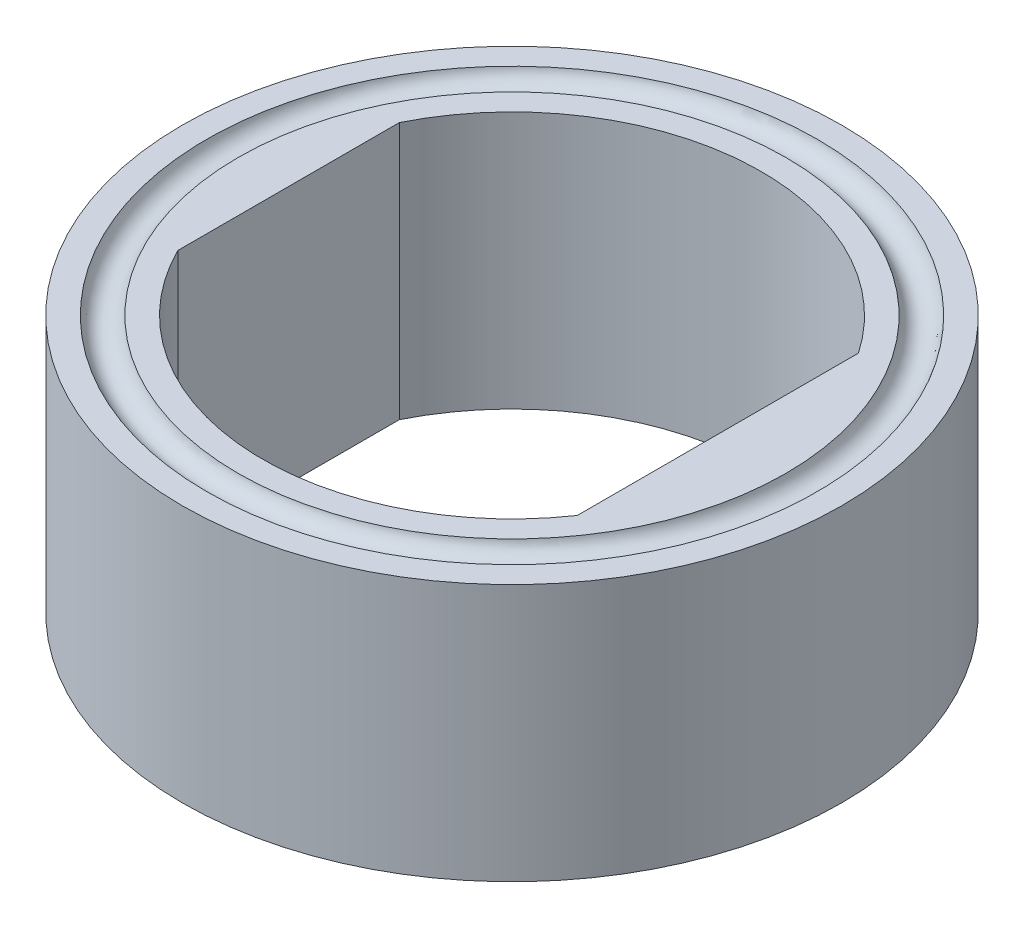
SolidWorks part; units mm, degrees
material "Markforged"
ref_plane "Front Plane" through (0, 0, 0) normal (0, 0, 1) x (1, 0, 0)
ref_plane "Top Plane" through (0, 0, 0) normal (0, 1, 0) x (1, 0, 0)
ref_plane "Right Plane" through (0, 0, 0) normal (1, 0, 0) x (0, 0, -1)
other "Bounding Box"
ref_plane "Default Plane" through (-8.9266, -12.7485, 0) normal (-0.1736, 0.9848, 0) x (0.9848, 0.1736, 0)
sketch "Sketch1" plane through (0, 0, 0) normal (0, 1, 0) x (1, 0, 0)
  circle A0 centre (0, 0) radius 65.0875
  circle A1 centre (0, 0) radius 49.2125
  dimension "D1" = 98.425
  dimension "D2" = 130.175
extrude "Boss-Extrude1" add sketch "Sketch1" along normal mid plane 50.8
sketch "Sketch11" plane through (0, 0, 0) normal (0, 0, 1) x (1, 0, 0)
  line L0 (49.2125, 25.4) -> (-49.2125, 25.4) construction
  line L1 (49.2125, 25.4) -> (-49.2125, 25.4) construction
  line L2 (49.2125, 25.4) -> (65.0875, 25.4) construction
  line L3 (57.15, 25.4) -> (57.15, 26.035) construction
  line L4 (0, 0) -> (0, 25.4) construction
  circle A0 centre (57.15, 26.035) radius 3.175
  dimension "D2" = 6.35
  dimension "D1" = 7.9375
  dimension "D3" = 0.635
revolve "Cut-Revolve1" cut sketch "Sketch11" angle 360 about L4
mirror "Mirror1" about plane through (0, 0, 0) normal (0, 1, 0) of "Cut-Revolve1"
sketch "Sketch3" plane through (0, 25.4, 0) normal (0, 1, 0) x (1, 0, 0)
  line L0 (-44.0944, -21.853) -> (-44.0944, 21.853)
  circle A0 centre (0, 0) radius 49.2125 construction
  arc A1 (-44.0944, 21.853) -> (-44.0944, -21.853) centre (0, 0) ccw
  dimension "D1" = 44.0944
extrude "Boss-Extrude2" add sketch "Sketch3" against normal through all
sketch "Sketch6" plane through (0, 25.4, 0) normal (0, 1, 0) x (1, 0, 0)
  line L0 (40.64, 27.7536) -> (40.64, -27.7536)
  arc A0 (-44.0944, -21.853) -> (-44.0944, 21.853) centre (0, 0) ccw construction
  arc A1 (40.64, 27.7536) -> (40.64, -27.7536) centre (0, 0) cw
  dimension "D1" = 40.64
extrude "Boss-Extrude4" add sketch "Sketch6" against normal through all
